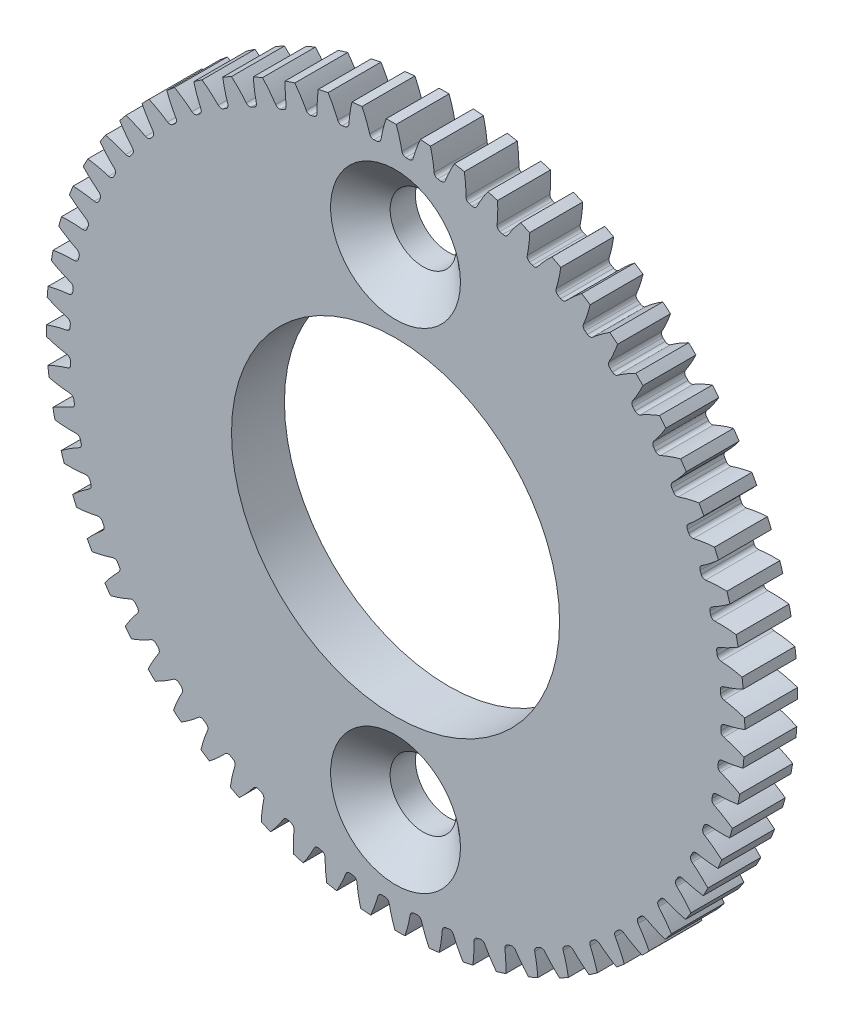
SolidWorks part; units mm, degrees
ref_plane "Front" through (0, 0, 0) normal (0, 0, 1) x (1, 0, 0)
ref_plane "Top" through (0, 0, 0) normal (0, 1, 0) x (1, 0, 0)
ref_plane "Right" through (0, 0, 0) normal (1, 0, 0) x (0, 0, -1)
sketch "Sketch3" plane through (0, 0, 0) normal (0, 0, 1) x (1, 0, 0)
  circle A0 centre (0, 0) radius 41.91
  dimension "od" = 83.82
extrude "gearBody" add sketch "Sketch3" along normal blind 6.35
sketch "Sketch2" plane through (0, 0, 0) normal (0, 0, 1) x (1, 0, 0)
  line L0 (0, 0) -> (36.3505, 15.0569) construction
  line L1 (49.1027, -9.5876) -> (0, 0) construction
  line L2 (0, 0) -> (36.3143, 0) construction
  line L3 (40.6371, -0.4885) -> (40.564, -2.485) construction
  line L5 (40.6005, -1.4868) -> (0, 0) construction
  line L7 (0, 0) -> (39.3455, 0) construction
  arc A0 (39.3376, -0.7896) -> (39.29, -2.0897) centre (0, 0) ccw construction
  arc A1 (41.9099, -0.0801) -> (41.8035, -2.9854) centre (0, 0) ccw construction
  arc A2 (40.6371, -0.4885) -> (40.564, -2.485) centre (0, 0) ccw construction
  arc A3 (39.0317, -1.6169) -> (39.0454, -1.2423) centre (0, 0) ccw
  arc A4 (49.1027, -9.5876) -> (39.399, -2.119) centre (35.1519, -17.6753) ccw
  arc A5 (49.1027, -9.5876) -> (49.6724, 5.9705) centre (0, 0) ccw
  arc A6 (49.6724, 5.9705) -> (39.4484, -0.7683) centre (36.3505, 15.0569) cw
  arc A7 (39.0454, -1.2423) -> (39.4484, -0.7683) centre (39.5443, -1.2582) cw
  arc A8 (39.399, -2.119) -> (39.0317, -1.6169) centre (39.5304, -1.6375) cw
  point P6 (49.6724, 5.9705)
  point P22 (49.1027, -9.5876)
  dimension "baseDia" = 78.691
  dimension "od" = 83.82
  dimension "pd" = 81.28
  dimension "rd" = 78.1304
  dimension "rFillet" = 0.4991
  dimension "pointX" = 49.6724
  dimension "pointY" = 5.9705
  dimension "CTT" = 1.9964
  dimension "flankCenterAngle" = 22.5
extrude "toothCut" cut sketch "Sketch2" along normal through all
pattern_circular "CirPattern1" count 64 over 360 about axis through (0, 0, 0) along (0, 0, 1) of "toothCut"
sketch "hub1Dia" plane through (0, 0, 0) normal (0, 0, -1) x (-1, 0, 0)
  circle A0 centre (0, 0) radius 25.4
  dimension "hub1Dia" = 50.8
extrude "hub1" [suppressed] add sketch "hub1Dia" along normal blind 19.05
sketch "hub2Dia" plane through (0, 0, 6.35) normal (0, 0, 1) x (1, 0, 0)
  circle A0 centre (0, 0) radius 21.844
  dimension "hub2dia" = 43.688
extrude "hub2" [suppressed] add sketch "hub2Dia" along normal blind 16.002
sketch "boreDia" plane through (0, 0, 0) normal (0, 0, 1) x (1, 0, 0)
  circle A0 centre (0, 0) radius 19.685
  circle A1 centre (0, 29.3687) radius 3.9688
  circle A2 centre (0, -29.3687) radius 3.9688
  dimension "D1" = 7.9375
  dimension "boreDia" = 39.37
  dimension "D2" = 29.3687
  dimension "D3" = 2
extrude "bore" cut sketch "boreDia" against normal mid plane 25.4
chamfer "hub2Chamfer" [suppressed] distance 0.508 angle 45
chamfer "hub2BoreChamfer" [suppressed] distance 0.508 angle 45
chamfer "hub1BoreChamfer" [suppressed] distance 0.508 angle 45
chamfer "hub1Chamfer" [suppressed] distance 0.508 angle 45
chamfer "BoreChamfer2" [suppressed] distance 0.508 angle 45
chamfer "boreChamfer1" [suppressed] distance 0.508 angle 45
chamfer "Chamfer2" distance 3.8227 angle 41 2 edges at (3.9688, -29.3687, 6.35) (3.9688, 29.3687, 6.35)
